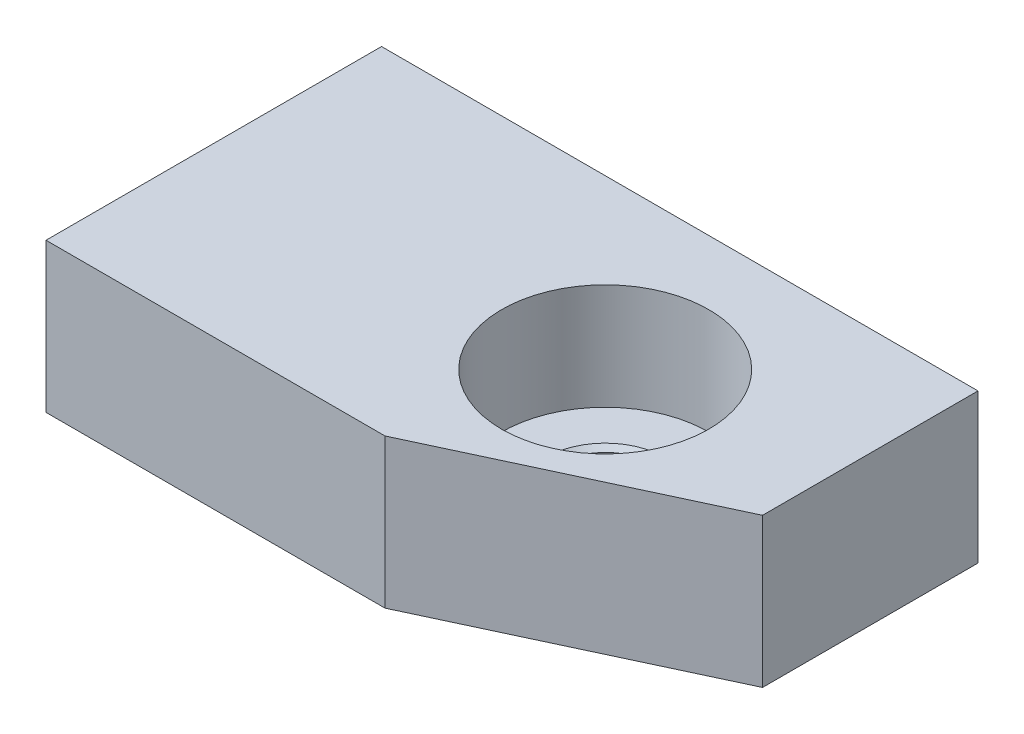
SolidWorks part; units mm, degrees
material "2024-T4"
ref_plane "Спереди" through (0, 0, 0) normal (0, 0, 1) x (1, 0, 0)
ref_plane "Сверху" through (0, 0, 0) normal (0, 1, 0) x (1, 0, 0)
ref_plane "Справа" through (0, 0, 0) normal (1, 0, 0) x (0, 0, -1)
sketch "Эскиз1" plane through (0, 0, 0) normal (0, 1, 0) x (1, 0, 0)
  line L0 (0, 0) -> (0, -9)
  line L1 (0, -9) -> (9.0939, -9)
  line L2 (16, -5.7796) -> (16, 0)
  line L3 (16, 0) -> (0, 0)
  line L4 (9.0939, -9) -> (16, -5.7796)
  dimension "D1" = 16
  dimension "D2" = 9
  dimension "D3" = 25
  dimension "D4" = 12
extrude "Бобышка-Вытянуть1" add sketch "Эскиз1" along normal blind 4
hole_wizard "Цековка для  винта с внутренним шестигранником #41" positions "Эскиз3" profile "Эскиз2" counterbore size "#4" standard "Ansi (в дюймах)" end condition through all
sketch "Эскиз3" plane through (0, 4, 0) normal (0, 1, 0) x (-1, 0, 0)
  line L0 (-16, 0) -> (0, 0) construction
  line L1 (0, 0) -> (0, 9) construction
  point P0 (-10.5, 4.5)
  dimension "D1" = 4.5
  dimension "D2" = 10.5
sketch "Эскиз2" plane through (10.5, 4, 4.5) normal (1, 0, 0) x (0, 0, 1)
  line L0 (0, 0) -> (0, 4)
  line L1 (1.4732, 3.873) -> (1.6002, 4)
  line L2 (1.4732, 3.873) -> (1.4732, 2.9718)
  line L3 (1.4732, 2.9718) -> (1.6002, 2.8448)
  line L4 (1.6002, 2.8448) -> (2.7788, 2.8448)
  line L5 (2.7788, 2.8448) -> (2.7788, 0)
  line L7 (2.7788, 0) -> (0, 0)
  line L9 (-1.4732, 2.9718) -> (-1.6002, 2.8448) construction
  line L11 (0, -6.35) -> (0, 107.95) construction
  line L12 (1.6002, 4) -> (0, 4)
  line L13 (-1.4732, 3.873) -> (-1.6002, 4) construction
  dimension "Диаметр сквозного отверстия" = 2.9464
  dimension "Глубина сквозного отверстия" = 4
  dimension "Диаметр цековки" = 5.5575
  dimension "Глубина цековки" = 2.8448
  dimension "Диаметр средней зенковки" = 3.2004
  dimension "Угол средней зенковки" = 90
  dimension "Диаметр задней зенковки" = 3.2004
  dimension "Угол задней зенковки" = 90
